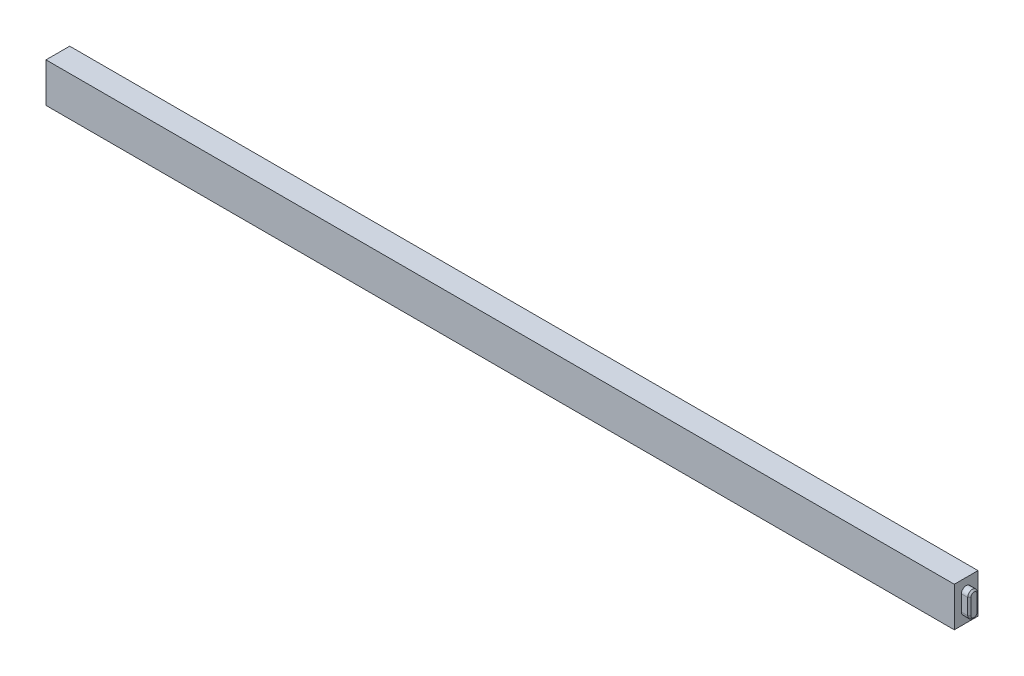
SolidWorks part; units mm, degrees
ref_plane "Plan de face" through (0, 0, 0) normal (0, 0, 1) x (1, 0, 0)
ref_plane "Plan de dessus" through (0, 0, 0) normal (0, 1, 0) x (1, 0, 0)
ref_plane "Plan de droite" through (0, 0, 0) normal (1, 0, 0) x (0, 0, -1)
sketch "Esquisse1" plane through (0, 0, 0) normal (0, 0, 1) x (1, 0, 0)
  line L1 (-575, 25) -> (575, 25)
  line L2 (-575, 25) -> (-575, -25)
  line L3 (-575, -25) -> (575, -25)
  line L4 (575, 25) -> (575, -25)
  line L5 (-575, 25) -> (575, -25) construction
  line L6 (-575, -25) -> (575, 25) construction
  point P0 (0, 0)
  dimension "D1" = 1150
  dimension "D2" = 50
extrude "Boss.-Extru.1" add sketch "Esquisse1" along normal blind 30
sketch "Esquisse2" plane through (575, 0, 0) normal (1, 0, 0) x (0, 0, -1)
  line L0 (-15, 10) -> (-15, -10) construction
  line L1 (-9, 10) -> (-9, -10)
  line L2 (-21, 10) -> (-21, -10)
  line L3 (0, -25) -> (0, 25) construction
  line L4 (-30, 25) -> (0, 25) construction
  arc A0 (-9, 10) -> (-21, 10) centre (-15, 10) ccw
  arc A1 (-21, -10) -> (-9, -10) centre (-15, -10) ccw
  point P2 (-15, 0)
  dimension "D1" = 6
  dimension "D2" = 15
  dimension "D3" = 20
  dimension "D4" = 25
extrude "Boss.-Extru.2" add sketch "Esquisse2" along normal blind 10
chamfer "Chanfrein1" distance 2 angle 45 4 edges at (585, 0, 9) (585, -16, 15) (585, 0, 21) (585, 16, 15)
sketch "Esquisse3" plane through (-575, 0, 0) normal (-1, 0, 0) x (0, 0, 1)
  line L0 (15, 10) -> (15, -10) construction
  line L1 (21, 10) -> (21, -10)
  line L2 (9, 10) -> (9, -10)
  line L4 (30, 25) -> (0, 25) construction
  line L5 (30, 25) -> (30, -25) construction
  arc A0 (21, 10) -> (9, 10) centre (15, 10) ccw
  arc A1 (9, -10) -> (21, -10) centre (15, -10) ccw
  point P2 (15, 0)
  dimension "D3" = 6
  dimension "D1" = 25
  dimension "D2" = 20
  dimension "D4" = 15
extrude "Boss.-Extru.3" add sketch "Esquisse3" along normal blind 10 contours L2 A1 L1 A0
chamfer "Chanfrein2" distance 2 angle 45 4 edges at (-585, 0, 21) (-585, -16, 15) (-585, 0, 9) (-585, 16, 15)
